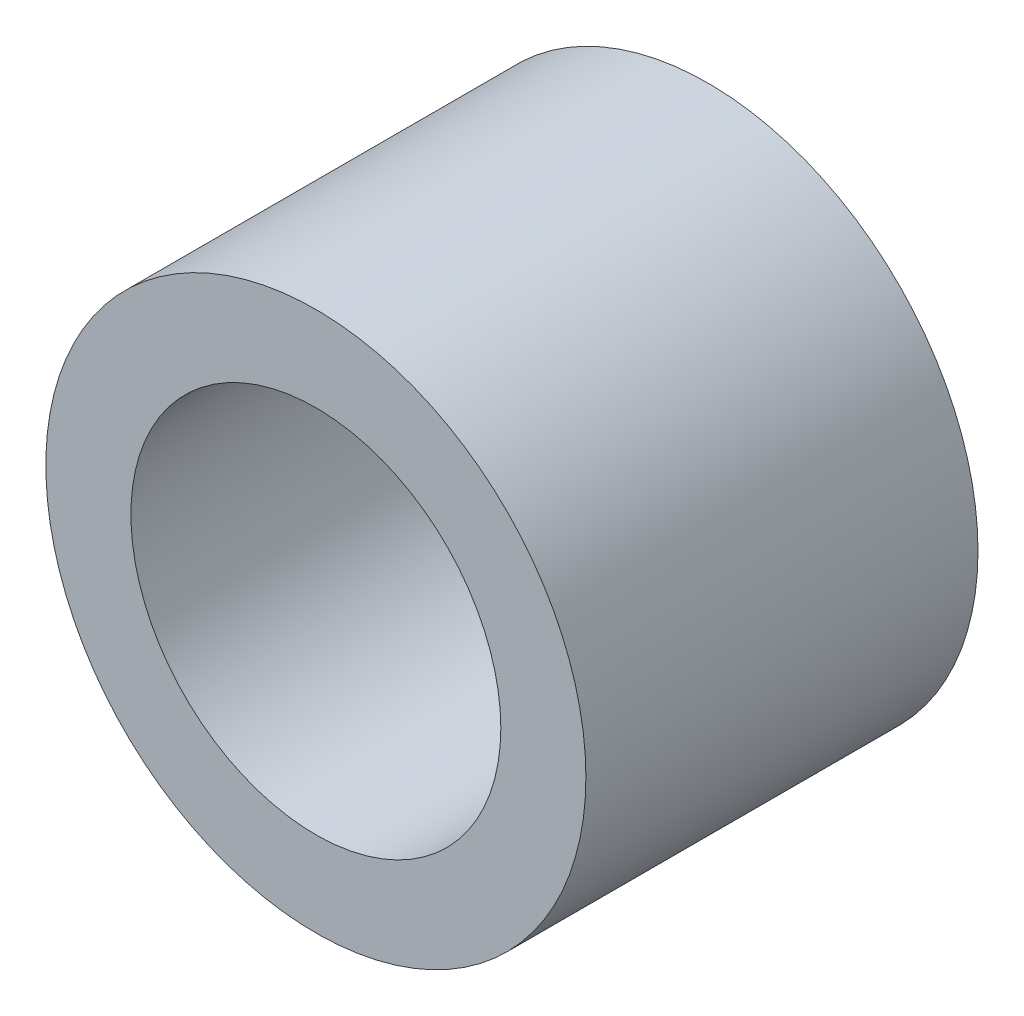
SolidWorks part; units mm, degrees
ref_plane "Ebene vorne" through (0, 0, 0) normal (0, 0, 1) x (1, 0, 0)
ref_plane "Ebene oben" through (0, 0, 0) normal (0, 1, 0) x (1, 0, 0)
ref_plane "Ebene rechts" through (0, 0, 0) normal (1, 0, 0) x (0, 0, -1)
sketch "Skizze1" plane through (0, 0, 0) normal (0, 0, 1) x (1, 0, 0)
  circle A0 centre (0, 0) radius 3.65
  circle A1 centre (0, 0) radius 2.5
  dimension "D1" = 7.3
  dimension "D2" = 5
extrude "Aufsatz-Linear austragen1" add sketch "Skizze1" along normal blind 5.3
